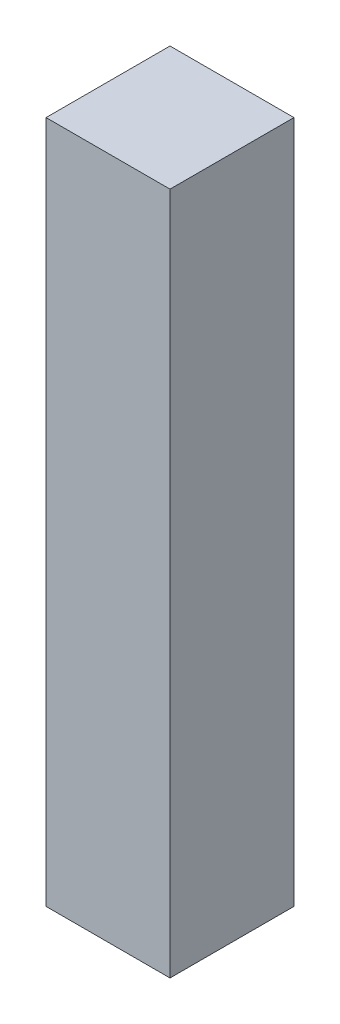
SolidWorks part; units mm, degrees
ref_plane "Front Plane" through (0, 0, 0) normal (0, 0, 1) x (1, 0, 0)
ref_plane "Top Plane" through (0, 0, 0) normal (0, 1, 0) x (1, 0, 0)
ref_plane "Right Plane" through (0, 0, 0) normal (1, 0, 0) x (0, 0, -1)
sketch "Sketch1" plane through (0, 0, 0) normal (0, 1, 0) x (1, 0, 0)
  line L1 (-1.27, 1.27) -> (1.27, 1.27)
  line L2 (-1.27, 1.27) -> (-1.27, -1.27)
  line L3 (-1.27, -1.27) -> (1.27, -1.27)
  line L4 (1.27, 1.27) -> (1.27, -1.27)
  line L5 (-1.27, 1.27) -> (1.27, -1.27) construction
  line L6 (-1.27, -1.27) -> (1.27, 1.27) construction
  point P0 (0, 0)
  dimension "D1" = 2.54
  dimension "D2" = 2.54
extrude "Boss-Extrude1" add sketch "Sketch1" along normal blind 14
